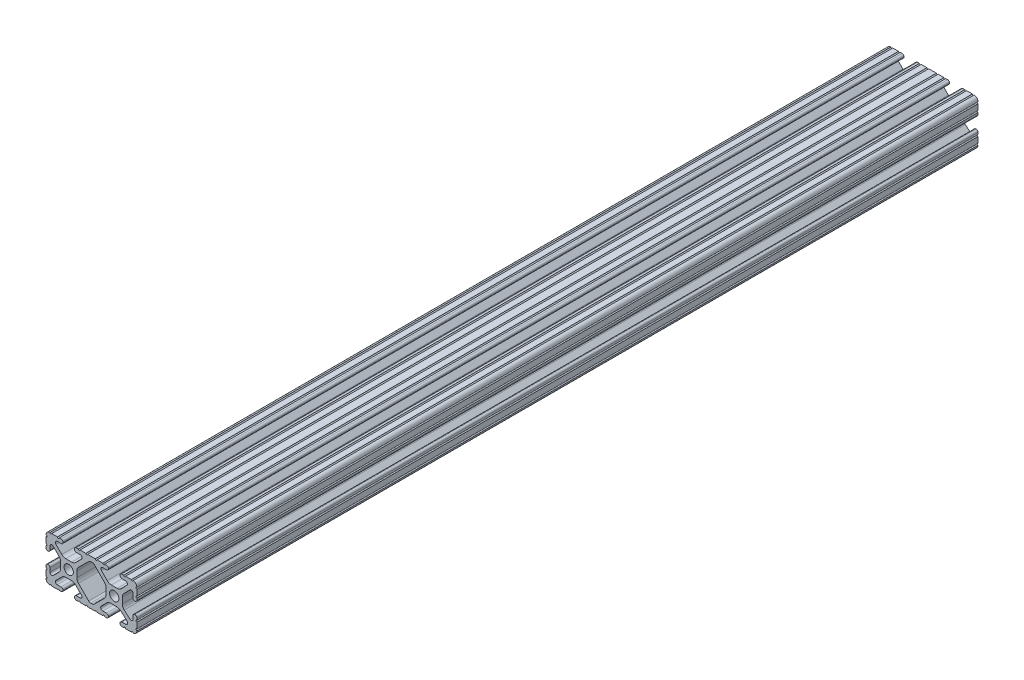
SolidWorks part; units mm, degrees
material "6105-T5 Aluminum"
ref_plane "Front Plane" through (0, 0, 0) normal (0, 0, 1) x (1, 0, 0)
ref_plane "Top Plane" through (0, 0, 0) normal (0, 1, 0) x (1, 0, 0)
ref_plane "Right Plane" through (0, 0, 0) normal (1, 0, 0) x (0, 0, -1)
sketch "Sketch1" plane through (0, 0, 0) normal (0, 0, 1) x (1, 0, 0)
  line L0 (0, 0) -> (0.0141, 4.4958) construction
  line L4 (-19.9595, -3.8694) -> (-14.2457, -9.5728)
  line L5 (-11.1543, -9.5728) -> (-5.4405, -3.8694)
  line L7 (-13.0952, 10.033) -> (-12.1485, 10.033)
  line L9 (-12.2668, -10.033) -> (-13.1332, -10.033)
  line L12 (-4.5085, -1.6223) -> (-4.5085, 1.6223)
  line L13 (-5.4171, 3.8459) -> (-11.0244, 9.5611)
  line L14 (-14.204, 9.5765) -> (-19.952, 3.8768)
  line L15 (-20.8915, 1.6223) -> (-20.8915, -1.6223)
  line L16 (9.5504, 12.7) -> (6.3331, 12.7)
  line L17 (5.3171, 12.7) -> (4.2875, 12.7)
  line L18 (3.2385, 11.651) -> (3.2385, 11.5392)
  line L19 (4.2875, 10.4902) -> (6.4164, 10.4902)
  line L20 (7.1441, 8.7652) -> (3.919, 5.4551)
  line L21 (1.6449, 4.4958) -> (-1.6167, 4.4958)
  line L22 (-3.883, 5.4472) -> (-7.1358, 8.7627)
  line L23 (-6.4106, 10.4902) -> (-4.2875, 10.4902)
  line L24 (-3.2385, 11.5392) -> (-3.2385, 11.651)
  line L25 (-4.2875, 12.7) -> (-5.3171, 12.7)
  line L26 (-6.3331, 12.7) -> (-9.5504, 12.7)
  line L27 (-10.5664, 12.7) -> (-14.8336, 12.7)
  line L28 (-15.8496, 12.7) -> (-19.0669, 12.7)
  line L29 (-20.0829, 12.7) -> (-21.1125, 12.7)
  line L30 (-22.1615, 11.651) -> (-22.1615, 11.5392)
  line L31 (-21.1125, 10.4902) -> (-18.9836, 10.4902)
  line L32 (-18.2326, 8.6661) -> (-21.51, 5.4163)
  line L33 (-23.7455, 4.4958) -> (-27.0545, 4.4958)
  line L34 (-29.29, 5.4163) -> (-32.5674, 8.6661)
  line L35 (-31.8164, 10.4902) -> (-29.6875, 10.4902)
  line L36 (-28.6385, 11.5392) -> (-28.6385, 11.651)
  line L37 (-29.6875, 12.7) -> (-30.7171, 12.7)
  line L38 (-31.7331, 12.7) -> (-34.9504, 12.7)
  line L39 (-38.1, 9.5504) -> (-38.1, 6.3331)
  line L40 (-38.1, 5.3171) -> (-38.1, 4.2375)
  line L41 (-37.101, 3.2385) -> (-36.9392, 3.2385)
  line L42 (-35.8902, 4.2875) -> (-35.8902, 6.3347)
  line L43 (-34.134, 7.0665) -> (-30.848, 3.8082)
  line L44 (-29.9085, 1.5536) -> (-29.9085, -1.6952)
  line L45 (-30.8405, -3.9423) -> (-34.1316, -7.2274)
  line L46 (-35.8902, -6.498) -> (-35.8902, -4.2875)
  line L47 (-36.9392, -3.2385) -> (-37.051, -3.2385)
  line L48 (-38.1, -4.2875) -> (-38.1, -5.3171)
  line L49 (-38.1, -6.3331) -> (-38.1, -9.5504)
  line L50 (-34.9504, -12.7) -> (-31.7331, -12.7)
  line L51 (-30.7171, -12.7) -> (-29.6875, -12.7)
  line L52 (-28.6384, -11.651) -> (-28.6384, -11.5392)
  line L53 (-29.6875, -10.4902) -> (-31.8164, -10.4902)
  line L54 (-32.5341, -8.7551) -> (-29.1966, -5.4237)
  line L55 (-26.9536, -4.4958) -> (-23.8464, -4.4958)
  line L56 (-21.6034, -5.4237) -> (-18.2659, -8.7551)
  line L57 (-18.9836, -10.4902) -> (-21.1125, -10.4902)
  line L58 (-22.1616, -11.5392) -> (-22.1616, -11.651)
  line L59 (-21.1125, -12.7) -> (-20.0829, -12.7)
  line L60 (-19.0669, -12.7) -> (-15.8496, -12.7)
  line L61 (-14.8336, -12.7) -> (-10.5664, -12.7)
  line L62 (-9.5504, -12.7) -> (-6.3331, -12.7)
  line L63 (-5.3171, -12.7) -> (-4.2875, -12.7)
  line L64 (-3.2384, -11.651) -> (-3.2384, -11.5392)
  line L65 (-4.2875, -10.4902) -> (-6.4106, -10.4902)
  line L66 (-7.2193, -8.5353) -> (-4.1021, -5.4237)
  line L67 (-1.8591, -4.4958) -> (1.4026, -4.4958)
  line L68 (3.4879, -5.2766) -> (7.1682, -8.4822)
  line L69 (6.4164, -10.4902) -> (4.2875, -10.4902)
  line L70 (3.2384, -11.5392) -> (3.2384, -11.651)
  line L71 (4.2875, -12.7) -> (5.3171, -12.7)
  line L72 (6.3331, -12.7) -> (9.5504, -12.7)
  line L73 (12.7, -9.5504) -> (12.7, -6.3331)
  line L74 (12.7, -5.3171) -> (12.7, -4.2375)
  line L75 (11.701, -3.2385) -> (11.4892, -3.2385)
  line L76 (10.4902, -4.2375) -> (10.4902, -6.1559)
  line L77 (8.884, -6.8869) -> (5.5982, -4.025)
  line L78 (4.5085, -1.6308) -> (4.5085, 1.6308)
  line L79 (5.4094, 3.8465) -> (8.8263, 7.3534)
  line L80 (10.4902, 6.6769) -> (10.4902, 4.2375)
  line L81 (11.4892, 3.2385) -> (11.701, 3.2385)
  line L82 (12.7, 4.2375) -> (12.7, 5.3171)
  line L83 (12.7, 6.3332) -> (12.7, 9.5504)
  circle A0 centre (-25.4, 0) radius 2.6035
  circle A1 centre (0, 0) radius 2.6035
  arc A2 (-13.0952, 10.033) -> (-14.204, 9.5765) centre (-13.0952, 8.4582) ccw
  arc A3 (-12.1485, 10.033) -> (-11.0244, 9.5611) centre (-12.1485, 8.4582) cw
  arc A4 (-20.8915, -1.6223) -> (-19.9595, -3.8694) centre (-17.7165, -1.6223) ccw
  arc A5 (-13.1332, -10.033) -> (-14.2457, -9.5728) centre (-13.1332, -8.4582) cw
  arc A6 (-5.4405, -3.8694) -> (-4.5085, -1.6223) centre (-7.6835, -1.6223) ccw
  arc A7 (-4.5085, 1.6223) -> (-5.4171, 3.8459) centre (-7.6835, 1.6223) ccw
  arc A8 (-12.2668, -10.033) -> (-11.1543, -9.5728) centre (-12.2668, -8.4582) ccw
  arc A9 (-19.952, 3.8768) -> (-20.8915, 1.6223) centre (-17.7165, 1.6223) ccw
  arc A16 (12.6998, 10.5664) -> (10.5664, 12.6998) centre (10.5918, 10.5918) ccw
  arc A17 (9.5504, 12.7) -> (10.5664, 12.6998) centre (10.0584, 12.7) ccw
  arc A18 (5.3171, 12.7) -> (6.3331, 12.7) centre (5.8251, 12.7) ccw
  arc A19 (4.2875, 12.7) -> (3.2385, 11.651) centre (4.2875, 11.651) ccw
  arc A20 (3.2385, 11.5392) -> (4.2875, 10.4902) centre (4.2875, 11.5392) ccw
  arc A21 (7.1441, 8.7652) -> (6.4164, 10.4902) centre (6.4164, 9.4742) ccw
  arc A22 (1.6449, 4.4958) -> (3.919, 5.4551) centre (1.6449, 7.6708) ccw
  arc A23 (-3.883, 5.4472) -> (-1.6167, 4.4958) centre (-1.6167, 7.6708) ccw
  arc A24 (-6.4106, 10.4902) -> (-7.1358, 8.7627) centre (-6.4106, 9.4742) ccw
  arc A25 (-4.2875, 10.4902) -> (-3.2385, 11.5392) centre (-4.2875, 11.5392) ccw
  arc A26 (-3.2385, 11.651) -> (-4.2875, 12.7) centre (-4.2875, 11.651) ccw
  arc A27 (-6.3331, 12.7) -> (-5.3171, 12.7) centre (-5.8251, 12.7) ccw
  arc A28 (-10.5664, 12.7) -> (-9.5504, 12.7) centre (-10.0584, 12.7) ccw
  arc A29 (-15.8496, 12.7) -> (-14.8336, 12.7) centre (-15.3416, 12.7) ccw
  arc A30 (-20.0829, 12.7) -> (-19.0669, 12.7) centre (-19.5749, 12.7) ccw
  arc A31 (-21.1125, 12.7) -> (-22.1615, 11.651) centre (-21.1125, 11.651) ccw
  arc A32 (-22.1615, 11.5392) -> (-21.1125, 10.4902) centre (-21.1125, 11.5392) ccw
  arc A33 (-18.2326, 8.6661) -> (-18.9836, 10.4902) centre (-18.9836, 9.4235) ccw
  arc A34 (-23.7455, 4.4958) -> (-21.51, 5.4163) centre (-23.7455, 7.6708) ccw
  arc A35 (-29.29, 5.4163) -> (-27.0545, 4.4958) centre (-27.0545, 7.6708) ccw
  arc A36 (-31.8164, 10.4902) -> (-32.5674, 8.6661) centre (-31.8164, 9.4235) ccw
  arc A37 (-29.6875, 10.4902) -> (-28.6385, 11.5392) centre (-29.6875, 11.5392) ccw
  arc A38 (-28.6385, 11.651) -> (-29.6875, 12.7) centre (-29.6875, 11.651) ccw
  arc A39 (-31.7331, 12.7) -> (-30.7171, 12.7) centre (-31.2251, 12.7) ccw
  arc A40 (-35.9664, 12.6998) -> (-34.9504, 12.7) centre (-35.4584, 12.7) ccw
  arc A41 (-35.9664, 12.6998) -> (-38.0998, 10.5664) centre (-35.9918, 10.5918) ccw
  arc A42 (-38.1, 9.5504) -> (-38.0998, 10.5664) centre (-38.1, 10.0584) ccw
  arc A43 (-38.1, 5.3171) -> (-38.1, 6.3331) centre (-38.1, 5.8251) ccw
  arc A44 (-38.1, 4.2375) -> (-37.101, 3.2385) centre (-37.101, 4.2375) ccw
  arc A45 (-36.9392, 3.2385) -> (-35.8902, 4.2875) centre (-36.9392, 4.2875) ccw
  arc A46 (-34.134, 7.0665) -> (-35.8902, 6.3347) centre (-34.8596, 6.3347) ccw
  arc A47 (-29.9085, 1.5536) -> (-30.848, 3.8082) centre (-33.0835, 1.5536) ccw
  arc A48 (-30.8405, -3.9423) -> (-29.9085, -1.6952) centre (-33.0835, -1.6952) ccw
  arc A49 (-35.8902, -6.498) -> (-34.1316, -7.2274) centre (-34.8596, -6.498) ccw
  arc A50 (-35.8902, -4.2875) -> (-36.9392, -3.2385) centre (-36.9392, -4.2875) ccw
  arc A51 (-37.051, -3.2385) -> (-38.1, -4.2875) centre (-37.051, -4.2875) ccw
  arc A52 (-38.1, -6.3331) -> (-38.1, -5.3171) centre (-38.1, -5.8251) ccw
  arc A53 (-38.0998, -10.5664) -> (-38.1, -9.5504) centre (-38.1, -10.0584) ccw
  arc A54 (-38.0998, -10.5664) -> (-35.9664, -12.6998) centre (-35.9918, -10.5918) ccw
  arc A55 (-34.9504, -12.7) -> (-35.9664, -12.6998) centre (-35.4584, -12.7) ccw
  arc A56 (-30.7171, -12.7) -> (-31.7331, -12.7) centre (-31.2251, -12.7) ccw
  arc A57 (-29.6875, -12.7) -> (-28.6384, -11.651) centre (-29.6875, -11.651) ccw
  arc A58 (-28.6384, -11.5392) -> (-29.6875, -10.4902) centre (-29.6875, -11.5392) ccw
  arc A59 (-32.5341, -8.7551) -> (-31.8164, -10.4902) centre (-31.8164, -9.4742) ccw
  arc A60 (-26.9536, -4.4958) -> (-29.1966, -5.4237) centre (-26.9536, -7.6708) ccw
  arc A61 (-21.6034, -5.4237) -> (-23.8464, -4.4958) centre (-23.8464, -7.6708) ccw
  arc A62 (-18.9836, -10.4902) -> (-18.2659, -8.7551) centre (-18.9836, -9.4742) ccw
  arc A63 (-21.1125, -10.4902) -> (-22.1616, -11.5392) centre (-21.1125, -11.5392) ccw
  arc A64 (-22.1616, -11.651) -> (-21.1125, -12.7) centre (-21.1125, -11.651) ccw
  arc A65 (-19.0669, -12.7) -> (-20.0829, -12.7) centre (-19.5749, -12.7) ccw
  arc A66 (-14.8336, -12.7) -> (-15.8496, -12.7) centre (-15.3416, -12.7) ccw
  arc A67 (-9.5504, -12.7) -> (-10.5664, -12.7) centre (-10.0584, -12.7) ccw
  arc A68 (-5.3171, -12.7) -> (-6.3331, -12.7) centre (-5.8251, -12.7) ccw
  arc A69 (-4.2875, -12.7) -> (-3.2384, -11.651) centre (-4.2875, -11.651) ccw
  arc A70 (-3.2384, -11.5392) -> (-4.2875, -10.4902) centre (-4.2875, -11.5392) ccw
  arc A71 (-7.2193, -8.5353) -> (-6.4106, -10.4902) centre (-6.4106, -9.3455) ccw
  arc A72 (-1.8591, -4.4958) -> (-4.1021, -5.4237) centre (-1.8591, -7.6708) ccw
  arc A73 (3.4879, -5.2766) -> (1.4026, -4.4958) centre (1.4026, -7.6708) ccw
  arc A74 (6.4164, -10.4902) -> (7.1682, -8.4822) centre (6.4164, -9.3455) ccw
  arc A75 (4.2875, -10.4902) -> (3.2384, -11.5392) centre (4.2875, -11.5392) ccw
  arc A76 (3.2384, -11.651) -> (4.2875, -12.7) centre (4.2875, -11.651) ccw
  arc A77 (6.3331, -12.7) -> (5.3171, -12.7) centre (5.8251, -12.7) ccw
  arc A78 (10.5664, -12.6998) -> (9.5504, -12.7) centre (10.0584, -12.7) ccw
  arc A79 (10.5664, -12.6998) -> (12.6998, -10.5664) centre (10.5918, -10.5918) ccw
  arc A80 (12.7, -9.5504) -> (12.6998, -10.5664) centre (12.7, -10.0584) ccw
  arc A81 (12.7, -5.3171) -> (12.7, -6.3331) centre (12.7, -5.8251) ccw
  arc A82 (12.7, -4.2375) -> (11.701, -3.2385) centre (11.701, -4.2375) ccw
  arc A83 (11.4892, -3.2385) -> (10.4902, -4.2375) centre (11.4892, -4.2375) ccw
  arc A84 (8.884, -6.8869) -> (10.4902, -6.1559) centre (9.5207, -6.1559) ccw
  arc A85 (4.5085, -1.6308) -> (5.5982, -4.025) centre (7.6835, -1.6308) ccw
  arc A86 (5.4094, 3.8465) -> (4.5085, 1.6308) centre (7.6835, 1.6308) ccw
  arc A87 (10.4902, 6.6769) -> (8.8263, 7.3534) centre (9.5207, 6.6769) ccw
  arc A88 (10.4902, 4.2375) -> (11.4892, 3.2385) centre (11.4892, 4.2375) ccw
  arc A89 (11.701, 3.2385) -> (12.7, 4.2375) centre (11.701, 4.2375) ccw
  arc A90 (12.7, 6.3332) -> (12.7, 5.3171) centre (12.7, 5.8251) ccw
  arc A91 (12.6998, 10.5664) -> (12.7, 9.5504) centre (12.7, 10.0584) ccw
  dimension "D1" = 5.207
  dimension "D6" = 6.477
  dimension "D7" = 14.859
  dimension "D14" = 1.5748
  dimension "D16" = 1.5748
  dimension "D15" = 3.175
  dimension "D3" = 50.8
  dimension "D4" = 25.4
  dimension "D5" = 8.2042
  dimension "D8" = 2.2098
  dimension "D9" = 2.2098
  dimension "D10" = 2.2098
  dimension "D11" = 2.2098
  dimension "D12" = 2.2098
  dimension "D13" = 6.477
extrude "Extrude1" add sketch "Sketch1" against normal mid plane 470
